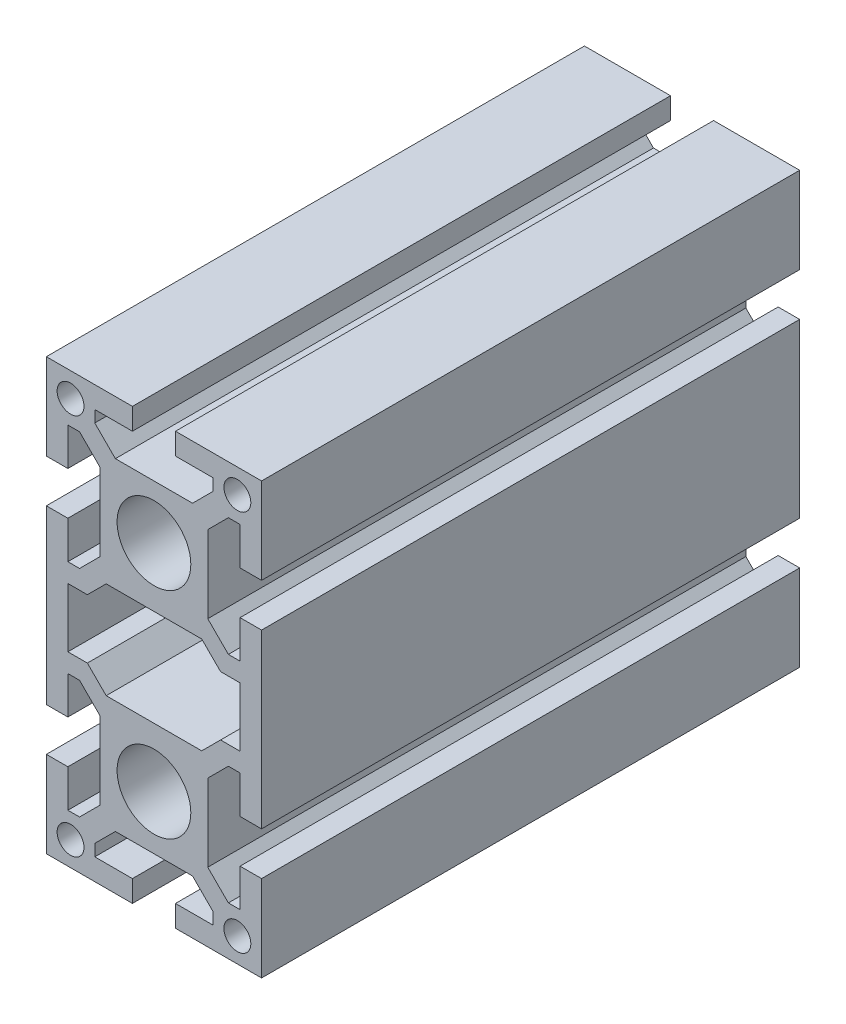
SolidWorks part; units mm, degrees
ref_plane "Front Plane" through (0, 0, 0) normal (0, 0, 1) x (1, 0, 0)
ref_plane "Top Plane" through (0, 0, 0) normal (0, 1, 0) x (1, 0, 0)
ref_plane "Right Plane" through (0, 0, 0) normal (1, 0, 0) x (0, 0, -1)
sketch "Sketch1" plane through (0, 0, 0) normal (0, 0, 1) x (1, 0, 0)
  line L76 (-8.8787, -9) -> (8.8787, -9)
  line L77 (8.8787, -9) -> (12.3787, -5.5)
  line L78 (12.3787, -5.5) -> (16, -5.5)
  line L79 (16, -5.5) -> (16, 5.5)
  line L80 (16, 5.5) -> (12.3787, 5.5)
  line L81 (12.3787, 5.5) -> (8.8787, 9)
  line L82 (8.8787, 9) -> (-8.8787, 9)
  line L83 (-8.8787, 9) -> (-12.3787, 5.5)
  line L84 (-12.3787, 5.5) -> (-16, 5.5)
  line L85 (-16, 5.5) -> (-16, -5.5)
  line L86 (-16, -5.5) -> (-12.3787, -5.5)
  line L87 (-12.3787, -5.5) -> (-8.8787, -9)
  line L88 (-20, -24) -> (-16, -24)
  line L89 (-16, -24) -> (-16, -31)
  line L90 (-16, -31) -> (-13.8284, -31)
  line L91 (-13.8284, -31) -> (-10, -27.1716)
  line L92 (-10, -27.1716) -> (-10, -12.8284)
  line L93 (-10, -12.8284) -> (-13.8284, -9)
  line L94 (-13.8284, -9) -> (-16, -9)
  line L95 (-16, -9) -> (-16, -16)
  line L96 (-16, -16) -> (-20, -16)
  line L97 (-20, -16) -> (-20, 16)
  line L98 (-20, 16) -> (-16, 16)
  line L99 (-16, 16) -> (-16, 9)
  line L100 (-16, 9) -> (-13.8284, 9)
  line L101 (-13.8284, 9) -> (-10, 12.8284)
  line L102 (-10, 12.8284) -> (-10, 27.1716)
  line L103 (-10, 27.1716) -> (-13.8284, 31)
  line L104 (-13.8284, 31) -> (-16, 31)
  line L105 (-16, 31) -> (-16, 24)
  line L106 (-16, 24) -> (-20, 24)
  line L107 (-20, 24) -> (-20, 40)
  line L108 (-20, 40) -> (-4, 40)
  line L109 (-4, 40) -> (-4, 36)
  line L110 (-4, 36) -> (-11, 36)
  line L111 (-11, 36) -> (-11, 33.8284)
  line L112 (-11, 33.8284) -> (-7.1716, 30)
  line L113 (-7.1716, 30) -> (7.1716, 30)
  line L114 (7.1716, 30) -> (11, 33.8284)
  line L115 (11, 33.8284) -> (11, 36)
  line L116 (11, 36) -> (4, 36)
  line L117 (4, 36) -> (4, 40)
  line L118 (4, 40) -> (20, 40)
  line L119 (20, 40) -> (20, 24)
  line L120 (20, 24) -> (16, 24)
  line L121 (16, 24) -> (16, 31)
  line L122 (16, 31) -> (13.8284, 31)
  line L123 (13.8284, 31) -> (10, 27.1716)
  line L124 (10, 27.1716) -> (10, 12.8284)
  line L125 (10, 12.8284) -> (13.8284, 9)
  line L126 (13.8284, 9) -> (16, 9)
  line L127 (16, 9) -> (16, 16)
  line L128 (16, 16) -> (20, 16)
  line L129 (20, 16) -> (20, -16)
  line L130 (20, -16) -> (16, -16)
  line L131 (16, -16) -> (16, -9)
  line L132 (16, -9) -> (13.8284, -9)
  line L133 (13.8284, -9) -> (10, -12.8284)
  line L134 (10, -12.8284) -> (10, -27.1716)
  line L135 (10, -27.1716) -> (13.8284, -31)
  line L136 (13.8284, -31) -> (16, -31)
  line L137 (16, -31) -> (16, -24)
  line L138 (16, -24) -> (20, -24)
  line L139 (20, -24) -> (20, -40)
  line L140 (20, -40) -> (4, -40)
  line L141 (4, -40) -> (4, -36)
  line L142 (4, -36) -> (11, -36)
  line L143 (11, -36) -> (11, -33.8284)
  line L144 (11, -33.8284) -> (7.1716, -30)
  line L145 (7.1716, -30) -> (-7.1716, -30)
  line L146 (-7.1716, -30) -> (-11, -33.8284)
  line L147 (-11, -33.8284) -> (-11, -36)
  line L148 (-11, -36) -> (-4, -36)
  line L149 (-4, -36) -> (-4, -40)
  line L150 (-4, -40) -> (-20, -40)
  line L151 (-20, -40) -> (-20, -24)
  circle A6 centre (-15.5, -35.5) radius 2.5
  circle A7 centre (-15.5, 35.5) radius 2.5
  circle A8 centre (15.5, -35.5) radius 2.5
  circle A9 centre (15.5, 35.5) radius 2.5
  circle A10 centre (0, -20) radius 6.85
  circle A11 centre (0, 20) radius 6.85
extrude "Extrude1" add sketch "Sketch1" against normal blind 100
